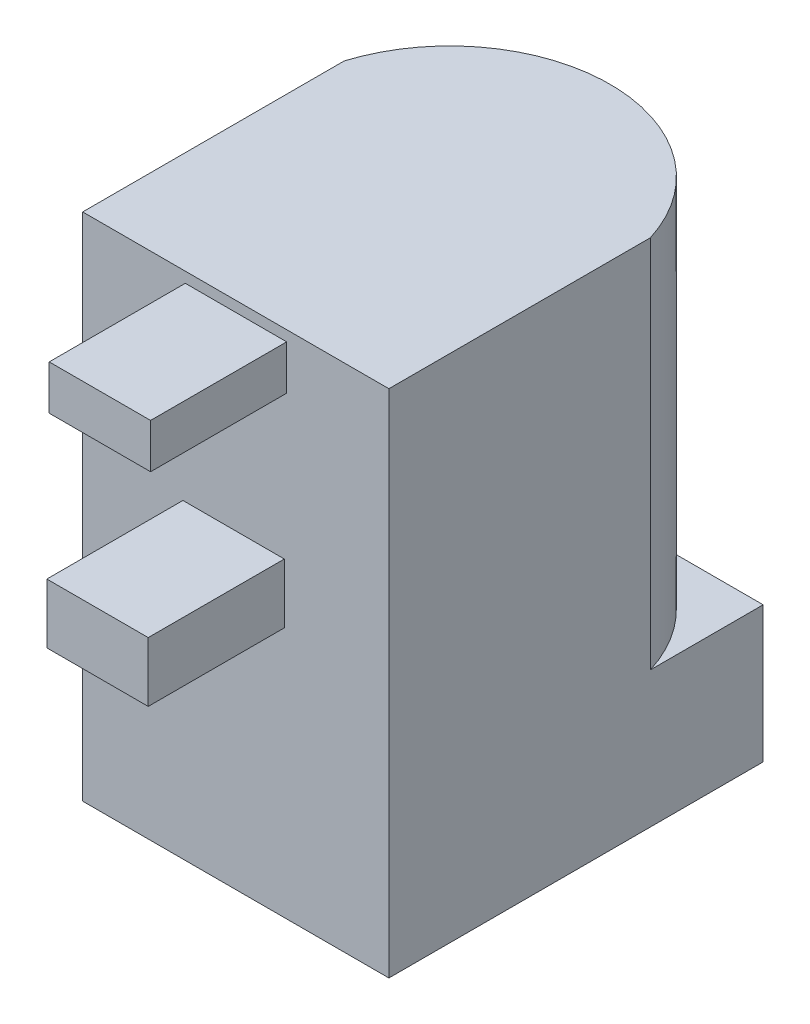
SolidWorks part; units mm, degrees
ref_plane "Front Plane" through (0, 0, 0) normal (0, 0, 1) x (1, 0, 0)
ref_plane "Top Plane" through (0, 0, 0) normal (0, 1, 0) x (1, 0, 0)
ref_plane "Right Plane" through (0, 0, 0) normal (1, 0, 0) x (0, 0, -1)
sketch "Sketch1" plane through (0, 0, 0) normal (0, 1, 0) x (1, 0, 0)
  line L1 (-3.8482, 5.6657) -> (5.1518, 5.6657)
  line L2 (-3.8482, 5.6657) -> (-3.8482, -5.3343)
  line L3 (-3.8482, -5.3343) -> (5.1518, -5.3343)
  line L4 (5.1518, 5.6657) -> (5.1518, -5.3343)
  dimension "D1" = 9
  dimension "D2" = 11
extrude "Boss-Extrude1" add sketch "Sketch1" along normal blind 15
sketch "Sketch2" plane through (0, 15, 0) normal (0, 1, 0) x (1, 0, 0)
  line L0 (-3.8482, 5.6657) -> (-3.8482, -5.3343) construction
  line L1 (5.1518, -5.3343) -> (5.1518, 5.6657) construction
  line L2 (-3.8482, 2.351) -> (-6.542, 7.0819)
  line L3 (-6.542, 7.0819) -> (7.0547, 6.8294)
  line L4 (7.0547, 6.8294) -> (5.1518, 2.351)
  arc A0 (-3.8482, 2.351) -> (5.1518, 2.351) centre (0.6518, 0.9538) cw
extrude "Cut-Extrude1" cut sketch "Sketch2" against normal blind 11
sketch "Sketch3" plane through (0, 0, 0) normal (0, -1, 0) x (1, 0, 0)
  line L0 (5.1518, -5.6657) -> (-3.8482, -5.6657) construction
  line L1 (5.1518, 5.3343) -> (5.1518, -5.6657) construction
  circle A0 centre (0.6518, -0.1657) radius 3.15
  dimension "D1" = 5.5
  dimension "D2" = 4.5
  dimension "D3" = 6.3
extrude "Cut-Extrude2" cut sketch "Sketch3" against normal blind 11
sketch "Sketch4" plane through (0, 0, 5.3343) normal (0, 0, 1) x (1, 0, 0)
  line L1 (-0.8324, 13.3838) -> (2.1475, 13.3838)
  line L2 (-0.8324, 13.3838) -> (-0.8324, 14.6905)
  line L3 (-0.8324, 14.6905) -> (2.1475, 14.6905)
  line L4 (2.1475, 13.3838) -> (2.1475, 14.6905)
  line L5 (-0.9019, 9.1284) -> (2.078, 9.1284)
  line L6 (-0.9019, 9.1284) -> (-0.9019, 7.3755)
  line L7 (-0.9019, 7.3755) -> (2.078, 7.3755)
  line L8 (2.078, 9.1284) -> (2.078, 7.3755)
extrude "Boss-Extrude2" add sketch "Sketch4" along normal blind 4
